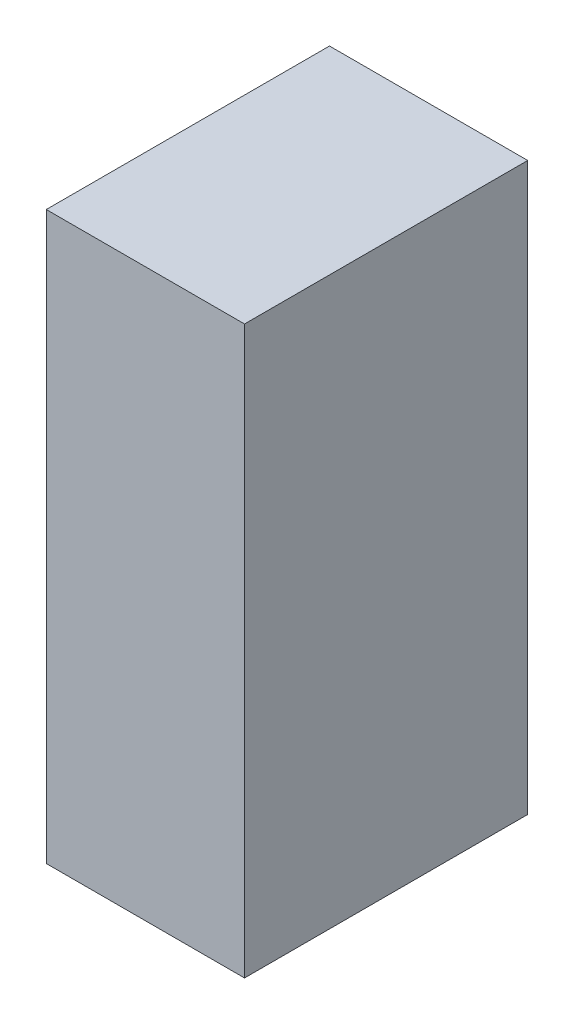
SolidWorks part; units mm, degrees
ref_plane "Piano frontale" through (0, 0, 0) normal (0, 0, 1) x (1, 0, 0)
ref_plane "Piano superiore" through (0, 0, 0) normal (0, 1, 0) x (1, 0, 0)
ref_plane "Piano destro" through (0, 0, 0) normal (1, 0, 0) x (0, 0, -1)
sketch "Schizzo1" plane through (0, 0, 0) normal (0, 0, 1) x (1, 0, 0)
  line L1 (-70, 0) -> (70, 0)
  line L2 (-70, 0) -> (-70, -400)
  line L3 (-70, -400) -> (70, -400)
  line L4 (70, 0) -> (70, -400)
  point P4 (0, 0)
  dimension "D1" = 140
  dimension "D2" = 400
extrude "Estrusione-Estrusione1" add sketch "Schizzo1" along normal blind 200
